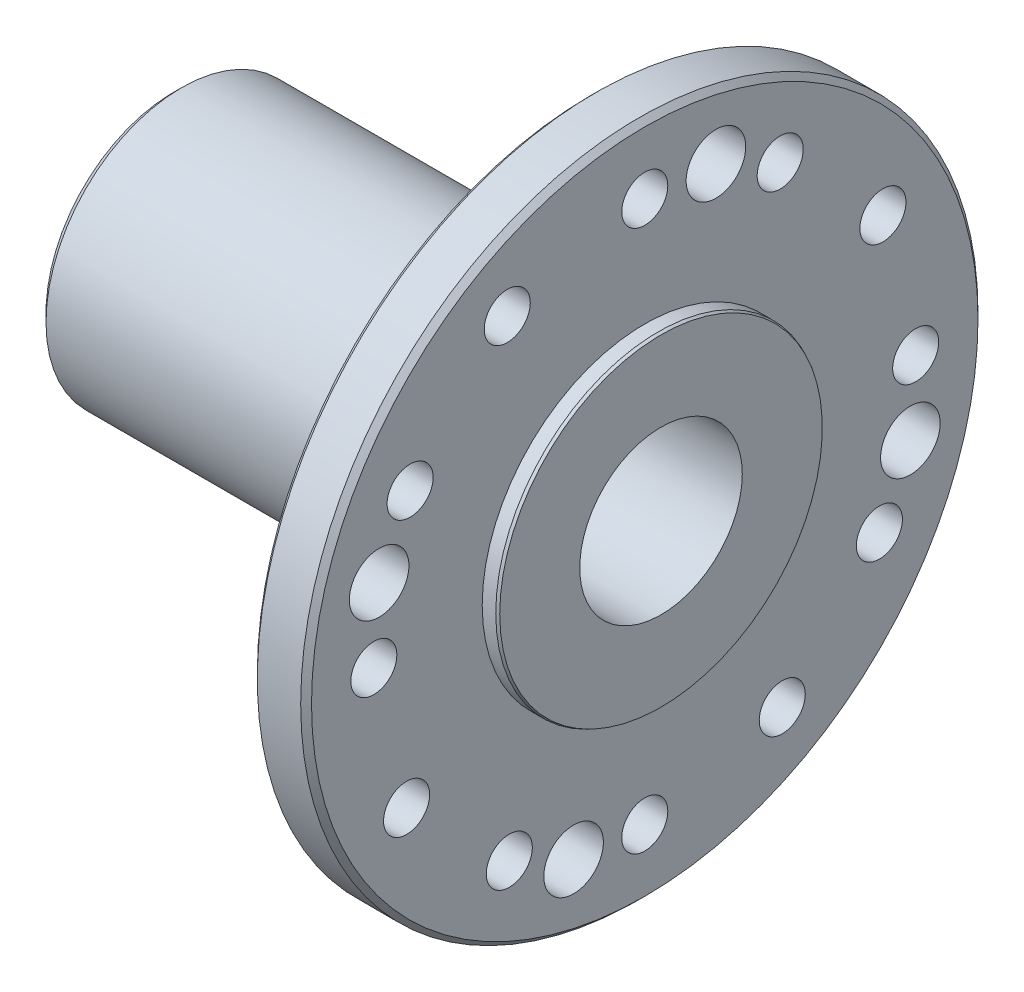
SolidWorks part; units mm, degrees
ref_plane "Ebene vorne" through (0, 0, 0) normal (0, 0, 1) x (1, 0, 0)
ref_plane "Ebene oben" through (0, 0, 0) normal (0, 1, 0) x (1, 0, 0)
ref_plane "Ebene rechts" through (0, 0, 0) normal (1, 0, 0) x (0, 0, -1)
sketch "Skizze17" plane through (0, 0, 0) normal (0, 0, 1) x (1, 0, 0)
  line L0 (0, 0) -> (0, -25)
  line L1 (0, -25) -> (72, -25)
  line L2 (77, -30) -> (77, -62.5)
  line L3 (77, -62.5) -> (87, -62.5)
  line L4 (87, -62.5) -> (87, -30)
  line L5 (87, -30) -> (90, -30)
  line L6 (90, -30) -> (90, 0)
  line L7 (90, 0) -> (0, 0)
  arc A0 (72, -25) -> (77, -30) centre (72, -30) cw
  dimension "D7" = 5
  dimension "D1" = 90
  dimension "D2" = 25
  dimension "D3" = 77
  dimension "D4" = 10
  dimension "D5" = 62.5
  dimension "D6" = 30
revolve "Rotation2" add sketch "Skizze17" angle 360 about L7
chamfer "Fase6" distance 1 angle 45 1 edges at (77, 0, -62.5)
chamfer "Fase7" distance 1 angle 45 1 edges at (87, 0, -62.5)
chamfer "Fase8" distance 1.5 angle 45 1 edges at (0, 0, -25)
chamfer "Fase9" distance 0.5 angle 25 1 edges at (90, 0, -30)
sketch "Skizze18" plane through (90, 0, 0) normal (1, 0, 0) x (0, 0, -1)
  circle A0 centre (0, 0) radius 15
  dimension "D1" = 30
extrude "Schnitt-Linear austragen5" cut sketch "Skizze18" against normal blind 60
sketch "Skizze19" plane through (30, 0, 0) normal (1, 0, 0) x (0, 0, -1)
  circle A0 centre (0, 0) radius 11.075
  dimension "D1" = 22.15
extrude "Schnitt-Linear austragen6" cut sketch "Skizze19" against normal through all
sketch "Skizze21" plane through (87, 0, 0) normal (1, 0, 0) x (0, 0, -1)
  circle A0 centre (0, 0) radius 50 construction
  circle A1 centre (0, 50) radius 4.25
  dimension "D1" = 100
  dimension "D2" = 8.5
extrude "Schnitt-Linear austragen7" cut sketch "Skizze21" against normal through all
sketch "Skizze22" plane through (87, 0, 0) normal (1, 0, 0) x (0, 0, -1)
  line L0 (0, 0) -> (0, 71.6565) construction
  line L1 (0, 0) -> (25, 43.3013) construction
  circle A0 centre (0, 0) radius 50 construction
  circle A1 centre (25, 43.3013) radius 4.25
  dimension "D1" = 100
  dimension "D2" = 8.5
  dimension "D3" = 30
  dimension "D4" = 25
  dimension "D5" = 43.3013
extrude "Schnitt-Linear austragen8" cut sketch "Skizze22" against normal through all contours A1
sketch "Skizze23" plane through (87, 0, 0) normal (1, 0, 0) x (0, 0, -1)
  line L0 (0, 0) -> (0, 72.8193) construction
  line L1 (13.1351, 49.0207) -> (0, 0) construction
  circle A0 centre (0, 0) radius 50.75 construction
  circle A1 centre (13.1351, 49.0207) radius 5.5
  dimension "D1" = 101.5
  dimension "D2" = 11
  dimension "D4" = 15
  dimension "D3" = 49.0207
  dimension "D5" = 13.1351
extrude "Schnitt-Linear austragen9" cut sketch "Skizze23" against normal through all
sketch "Skizze36" plane through (87, 0, 0) normal (1, 0, 0) x (0, 0, -1)
  line L0 (0, 0) -> (43.9508, 25.375) construction
  line L1 (0, 0) -> (45.3197, 0) construction
  circle A0 centre (43.9508, 25.375) radius 4.25
  circle A1 centre (0, 0) radius 50.75 construction
  dimension "D1" = 8.5
  dimension "D4" = 101.5
  dimension "D2" = 25.375
  dimension "D3" = 43.9508
  dimension "D5" = 30
extrude "Schnitt-Linear austragen10" cut sketch "Skizze36" against normal through all
pattern_circular "Kreismuster42" count 4 over 360 about axis through (0, 0, 0) along (1, 0, 0) of "Schnitt-Linear austragen7", "Schnitt-Linear austragen8", "Schnitt-Linear austragen9", "Schnitt-Linear austragen10"
sketch "Skizze34" plane through (0, 0, 0) normal (-1, 0, 0) x (0, 0, 1)
  line L0 (0, 21.9457) -> (0, -19.8341) construction
  line L1 (-21.71, 0) -> (21.71, 0) construction
  line L2 (-0.9987, 11.075) -> (-0.55, 10.175)
  line L3 (-0.55, 10.175) -> (0.55, 10.175)
  line L4 (0.55, 10.175) -> (0.9987, 11.075)
  line L5 (0.9987, 11.075) -> (-0.9987, 11.075)
  circle A1 centre (0, 0) radius 11.075 construction
  point P6 (0, 0)
  point P9 (0, 11.075)
  dimension "D1" = 53
  dimension "D2" = 20.35
  dimension "D3" = 1.1
extrude "Aufsatz-Linear austragen8" add sketch "Skizze34" against normal blind 30
pattern_circular "Kreismuster41" count 28 over 360 about axis through (0, 0, 0) along (1, 0, 0) of "Aufsatz-Linear austragen8"
sketch "Skizze35" plane through (0, 0, 0) normal (0, 1, 0) x (1, 0, 0)
  line L0 (0, 0) -> (30, 0) construction
  line L1 (0, 11.25) -> (11.25, 0)
  line L2 (0, 23.5) -> (0, -23.5) construction
  line L3 (11.25, 0) -> (0, 0)
  line L4 (0, 0) -> (0, 11.25)
  line L5 (18.75, 0) -> (30, 0)
  line L6 (30, 0) -> (30, 11.25)
  line L7 (30, 11.25) -> (18.75, 0)
  line L8 (30, -15) -> (30, 15) construction
  dimension "D1" = 45
  dimension "D2" = 22.5
revolve "Schnitt-Rotation1" cut sketch "Skizze35" angle 360 about L0
